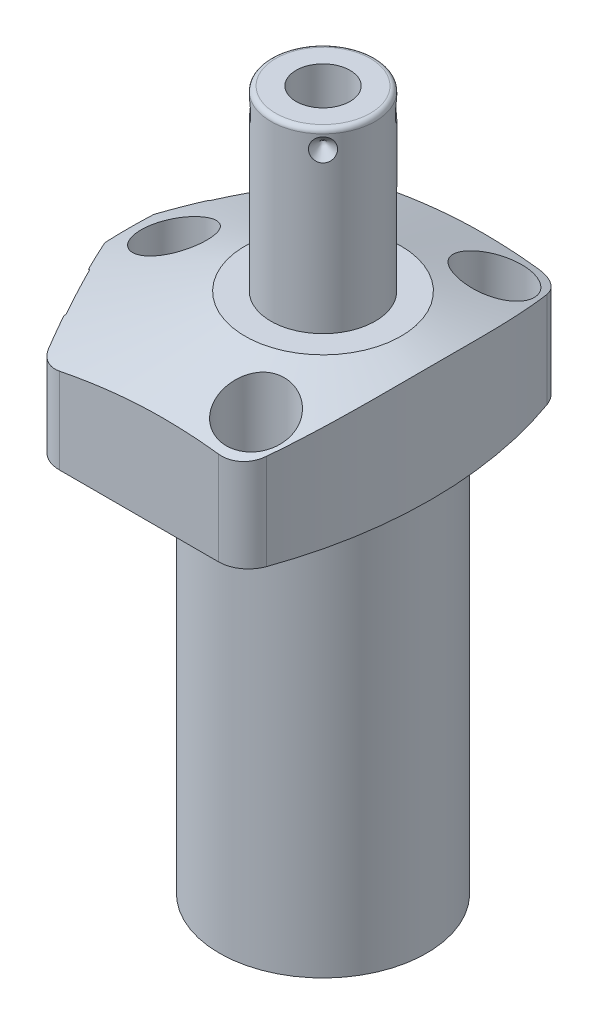
SolidWorks part; units mm, degrees
material "Alloy Steel"
ref_plane "Front Plane" through (0, 0, 0) normal (0, 0, 1) x (1, 0, 0)
ref_plane "Top Plane" through (0, 0, 0) normal (0, 1, 0) x (1, 0, 0)
ref_plane "Right Plane" through (0, 0, 0) normal (1, 0, 0) x (0, 0, -1)
ref_plane "Plane1" through (0, 0, 0) normal (0, 0, 1) x (0, -1, 0)
sketch "Sketch1" plane through (0, 0, 0) normal (0, 0, 1) x (0, -1, 0)
  line L0 (0, 44.45) -> (-26.9748, 44.45)
  line L1 (-26.9748, 44.45) -> (-26.9748, 0)
  line L2 (-26.9748, 0) -> (84.1502, 0)
  line L3 (84.1502, 0) -> (84.1502, 22.098)
  line L4 (84.1502, 22.098) -> (0, 22.098)
  line L5 (0, 22.098) -> (0, 44.45)
  line L6 (-32.531, 0) -> (89.7065, 0) construction
  dimension "D1" = 111.125
  dimension "D2" = 26.9748
  dimension "D3" = 88.9
  dimension "D4" = 44.196
revolve "Revolve1" add sketch "Sketch1" angle 360 about L6
ref_plane "Plane2" through (0, 0, 0) normal (0, -1, 0) x (0, 0, -1)
sketch "Sketch2" plane through (0, 0, 0) normal (0, -1, 0) x (0, 0, -1)
  line L0 (34.1122, -28.4984) -> (34.1122, 28.4984)
  line L2 (-34.1122, 28.4984) -> (-34.1122, -28.4984)
  line L3 (0, -32.1458) -> (0, 48.0974) construction
  arc A0 (34.1122, -28.4984) -> (34.1122, 28.4984) centre (0, 0) ccw
  circle A1 centre (0, 0) radius 44.45
  arc A2 (-34.1122, 28.4984) -> (-34.1122, -28.4984) centre (0, 0) ccw
  point P4 (0, 0)
  dimension "D1" = 68.2244
  dimension "D2" = 0
extrude "Cut-Extrude1" cut sketch "Sketch2" against normal up to next
ref_plane "Plane3" through (0, 0, 0) normal (0, -1, 0) x (-1, 0, 0)
sketch "Sketch3" plane through (0, 0, 0) normal (0, -1, 0) x (-1, 0, 0)
  line L0 (25.9049, 34.1122) -> (44.0427, 0)
  line L1 (44.0427, 0) -> (25.9049, -34.1122)
  line L2 (-39.4859, -20.995) -> (73.8214, 39.2515) construction
  line L3 (0, 0) -> (44.0427, 0) construction
  line L6 (-28.4984, -34.1122) -> (28.4984, -34.1122)
  line L7 (28.4984, 34.1122) -> (-28.4984, 34.1122)
  line L8 (25.9049, -34.1122) -> (28.4984, -34.1122)
  line L9 (28.4984, 34.1122) -> (25.9049, 34.1122)
  arc A2 (-28.4984, 34.1122) -> (-28.4984, -34.1122) centre (0, 0) ccw
  arc A3 (28.4984, -34.1122) -> (28.4984, 34.1122) centre (0, 0) ccw
  arc A5 (28.4984, -34.1122) -> (28.4984, 34.1122) centre (0, 0) ccw
  dimension "D1" = 28
  dimension "D2" = 38.8874
  dimension "D3" = 0
extrude "Cut-Extrude2" cut sketch "Sketch3" against normal up to next
ref_plane "Plane4" through (0, 0, 0) normal (0, -1, 0) x (-1, 0, 0)
sketch "S2D0002" plane through (0, 0, 0) normal (0, -1, 0) x (-1, 0, 0)
  line L0 (41.275, 85.425) -> (41.275, -85.425)
  arc A0 (41.275, 85.425) -> (41.275, -85.425) centre (65.8876, 0) ccw
  dimension "D3" = 88.9
  dimension "D1" = 65.8876
  dimension "D2" = 41.275
extrude "Cut-Extrude3" cut sketch "S2D0002" against normal blind 38.0873 flip side to cut
fillet "Fillet1" radius 6.35 2 edges at (16.2073, 13.4874, 34.1122) (16.2073, 13.4874, -34.1122)
fillet "Fillet2" radius 6.35 1 edges at (-25.9049, 13.4874, 34.1122)
fillet "Fillet3" radius 6.35 1 edges at (-25.9049, 13.4874, -34.1122)
ref_plane "Plane5" through (0, 0, 0) normal (0, 0, 1) x (1, 0, 0)
sketch "Sketch5" plane through (0, 0, 0) normal (0, 0, 1) x (1, 0, 0)
  line L0 (-16.637, 26.9748) -> (-47.625, 15.6961)
  line L1 (0, 7.6649) -> (0, 27.5963) construction
  line L3 (11.854, 26.9748) -> (-22.0895, 26.9748) construction
  line L4 (-16.637, 26.9748) -> (-47.625, 26.9748)
  line L5 (-47.625, 26.9748) -> (-47.625, 15.6961)
  dimension "D1" = 33.274
  dimension "D2" = 20
  dimension "D3" = 47.625
revolve "Cut-Revolve1" cut sketch "Sketch5" angle 360 about L1
ref_plane "Plane6" through (-34.1113, 10.287, -18.1373) normal (0, 1, 0) x (0.4695, 0, -0.8829)
sketch "Sketch6" plane through (-34.1113, 10.287, -18.1373) normal (0, 1, 0) x (0.4695, 0, -0.8829)
  line L0 (0, 0) -> (6.1849, 0)
  line L1 (6.1849, 0) -> (5.6423, -2.5527)
  line L2 (5.6423, -2.5527) -> (4.9784, -3.2166)
  line L3 (4.9784, -3.2166) -> (4.9784, -15.748)
  line L4 (4.9784, -15.748) -> (0, -15.748)
  line L5 (0, -15.748) -> (0, 0)
  line L6 (0, -16.5354) -> (0, 0.7874) construction
  dimension "D1" = 15.748
revolve "Cut-Revolve2" cut sketch "Sketch6" angle 360 about L6
ref_plane "Plane7" through (-34.1113, 10.287, 18.1373) normal (0, 1, 0) x (-0.4695, 0, -0.8829)
sketch "Sketch7" plane through (-34.1113, 10.287, 18.1373) normal (0, 1, 0) x (-0.4695, 0, -0.8829)
  line L0 (0, 0) -> (6.1849, 0)
  line L1 (6.1849, 0) -> (5.6423, -2.5527)
  line L2 (5.6423, -2.5527) -> (4.9784, -3.2166)
  line L3 (4.9784, -3.2166) -> (4.9784, -15.748)
  line L4 (4.9784, -15.748) -> (0, -15.748)
  line L5 (0, -15.748) -> (0, 0)
  line L6 (0, -16.5354) -> (0, 0.7874) construction
  dimension "D1" = 15.748
revolve "Cut-Revolve3" cut sketch "Sketch7" angle 360 about L6
ref_plane "Plane8" through (-13.4874, 2.667, -26.5938) normal (0, 0, 1) x (-1, 0, 0)
sketch "Sketch8" plane through (-13.4874, 2.667, -26.5938) normal (0, 0, 1) x (-1, 0, 0)
  line L0 (0, 0) -> (4.5466, 0)
  line L1 (4.5466, 0) -> (4.1066, -2.0701)
  line L2 (4.1066, -2.0701) -> (3.4544, -2.7223)
  line L3 (3.4544, -2.7223) -> (3.4544, -12.573)
  line L4 (3.4544, -12.573) -> (0, -12.573)
  line L5 (0, -12.573) -> (0, 0)
  line L6 (0, -13.2017) -> (0, 0.6287) construction
  dimension "D1" = 12.573
revolve "Cut-Revolve4" cut sketch "Sketch8" angle 360 about L6
ref_plane "Plane9" through (-13.4874, 2.667, 26.5938) normal (0, 0, 1) x (-1, 0, 0)
sketch "Sketch9" plane through (-13.4874, 2.667, 26.5938) normal (0, 0, 1) x (-1, 0, 0)
  line L0 (0, 0) -> (4.5466, 0)
  line L1 (4.5466, 0) -> (4.1066, -2.0701)
  line L2 (4.1066, -2.0701) -> (3.4544, -2.7223)
  line L3 (3.4544, -2.7223) -> (3.4544, -12.573)
  line L4 (3.4544, -12.573) -> (0, -12.573)
  line L5 (0, -12.573) -> (0, 0)
  line L6 (0, -13.2017) -> (0, 0.6287) construction
  dimension "D1" = 12.573
revolve "Cut-Revolve5" cut sketch "Sketch9" angle 360 about L6
sketch "Sketch17" plane through (-34.3355, 0, 18.2565) normal (-0.8829, 0, 0.4695) x (0.4695, 0, 0.8829)
  circle A0 centre (0, 10.287) radius 10.4775
  dimension "D1" = 20.955
extrude "Cut-Extrude4" cut sketch "Sketch17" against normal blind 0.254
sketch "Sketch18" plane through (0, 0, 0) normal (0, -1, 0) x (1, 0, 0)
  circle A0 centre (-13.4874, 26.5938) radius 5.5626
  dimension "D1" = 11.1252
extrude "Cut-Extrude5" cut sketch "Sketch18" against normal blind 2.667
mirror "Mirror1" about plane through (0, 0, 0) normal (0, 0, 1) of "Cut-Extrude5", "Cut-Extrude4"
ref_plane "Plane10" through (0, 0, 0) normal (1, 0, 0) x (0, 0, -1)
sketch "Sketch10" plane through (0, 0, 0) normal (1, 0, 0) x (0, 0, -1)
  line L0 (0, 26.9748) -> (-11.1125, 26.9748)
  line L1 (-11.1125, 26.9748) -> (-11.1125, 63.8302)
  line L2 (-10.0965, 64.8462) -> (0, 64.8462)
  line L3 (0, 64.8462) -> (0, 26.9748)
  line L4 (0, 14.3517) -> (0, 66.7398) construction
  line L5 (16.637, 26.9748) -> (-16.637, 26.9748) construction
  line L6 (-29.8978, 0) -> (29.8978, 0) construction
  arc A0 (-10.0965, 64.8462) -> (-11.1125, 63.8302) centre (-10.0965, 63.8302) ccw
  dimension "D2" = 1.016
  dimension "D1" = 64.8462
  dimension "D3" = 22.225
revolve "Revolve2" add sketch "Sketch10" angle 360 about L4
ref_plane "Plane11" through (5.7531, 64.8462, 0) normal (0, 0, 1) x (1, 0, 0)
sketch "S2D0001" plane through (5.7531, 64.8462, 0) normal (0, 0, 1) x (1, 0, 0)
  line L0 (0, 0) -> (0, -17.018)
  line L1 (0, -17.018) -> (-5.7531, -20.4748)
  line L2 (0, 0) -> (-5.7531, 0)
  line L3 (-5.7531, 0) -> (-5.7531, -20.4748)
  line L4 (-5.7531, -27.7363) -> (-5.7531, 1.0237) construction
  line L5 (4.3434, 0) -> (-15.8496, 0) construction
  dimension "D1" = 11.5062
  dimension "D2" = 17.018
  dimension "D3" = 59
revolve "Cut-Revolve6" cut sketch "S2D0001" angle 360 about L4
sketch "Sketch12" plane through (-34.1113, 0, -18.1373) normal (-0.8829, 0, -0.4695) x (-0.4695, 0, 0.8829)
  circle A0 centre (0, 10.287) radius 6.4389
  circle A1 centre (0, 10.287) radius 4.9784 construction
  dimension "D1" = 12.8778
extrude "Extrude1" add sketch "Sketch12" along normal blind 1.651
sketch "Sketch13" plane through (0, 0, 0) normal (0, -1, 0) x (1, 0, 0)
  circle A0 centre (-13.4874, -26.5938) radius 4.8006
  circle A1 centre (-13.4874, -26.5938) radius 3.4544 construction
  dimension "D1" = 9.6012
ref_plane "Plane12" through (-13.4874, 2.667, -26.5938) normal (0, 1, 0) x (-1, 0, 0)
extrude "Extrude2" add sketch "Sketch13" against normal up to surface
ref_plane "Plane13" through (-13.4874, 0, 26.5938) normal (1, 0, 0) x (0, 0, -1)
sketch "Sketch14" plane through (-13.4874, 0, 26.5938) normal (1, 0, 0) x (0, 0, -1)
  line L0 (5.461, 2.667) -> (5.461, 0.9398)
  line L1 (5.461, 0.9398) -> (5.3016, 0.9398)
  line L2 (2.667, 0.4318) -> (2.667, 0.127)
  line L3 (2.667, 0.127) -> (1.5875, 0.127)
  line L4 (1.5875, 0.127) -> (1.5875, 10.6172)
  line L5 (1.5875, 10.6172) -> (3.2512, 10.6172)
  line L6 (3.2512, 10.6172) -> (3.2512, 2.667)
  line L7 (3.2512, 2.667) -> (5.461, 2.667)
  line L8 (3.175, 0.9398) -> (3.8424, 0.9398)
  line L9 (0, -1.0109) -> (0, 11.1709) construction
  arc A0 (3.175, 0.9398) -> (2.667, 0.4318) centre (3.175, 0.4318) ccw
  arc A1 (3.8424, 0.9398) -> (5.3016, 0.9398) centre (4.572, 0.4318) ccw
  dimension "D1" = 2.54
  dimension "D2" = 7.9502
revolve "Revolve3" add sketch "Sketch14" angle 360 about L9
ref_plane "Plane14" through (-11.1125, 60.8838, 0) normal (0, 0, 1) x (0, 1, 0)
ref_plane "Plane15" through (0, 0, 0) normal (-0.7071, 0, 0.7071) x (0.7071, 0, 0.7071)
sketch "Sketch15" plane through (-7.8577, 60.8838, -7.8577) normal (-0.7071, 0, 0.7071) x (0, 1, 0)
  line L0 (0, 0) -> (2.413, 0)
  line L1 (2.413, 0) -> (0, -2.413)
  line L2 (0, 0) -> (0, -2.413)
  line L3 (0, -5.1094) -> (0, 0.1207) construction
  line L4 (2.9464, 0) -> (-33.909, 0) construction
  line L5 (3.9624, -21.209) -> (3.9624, -1.016) construction
  dimension "D1" = 3.9624
  dimension "D2" = 4.826
  dimension "D3" = 45
revolve "Cut-Revolve7" cut sketch "Sketch15" angle 360 about L3
pattern_circular "CirPattern1" count 4 over 360 about axis through (0, 14.3517, 0) along (0, -1, 0) of "Cut-Revolve7"
hole_wizard "Hole1" positions "Sketch20" profile "Sketch19" legacy end condition up to next
sketch "Sketch20" plane through (0, 26.9748, 0) normal (0, 1, 0) x (-1, 0, 0)
  line L0 (0, 0) -> (47.6205, 0) construction
  line L1 (0, 0) -> (0, 38.9977) construction
  point P0 (-11.1252, -25.4)
  point P10 (31.75, 0)
  point P14 (-11.1252, 25.4)
  dimension "D1" = 11.1252
  dimension "D2" = 25.4
  dimension "D3" = 31.75
sketch "Sketch19" plane through (11.1252, 26.9748, -25.4) normal (1, 0, 0) x (0, 0, 1)
  line L0 (0, 0) -> (0, 26.9748)
  line L1 (0, 26.9748) -> (4.3688, 26.9748)
  line L2 (4.3688, 26.9748) -> (4.3688, 16.6624)
  line L3 (4.3688, 16.6624) -> (6.9977, 16.6624)
  line L4 (6.9977, 16.6624) -> (6.9977, 0)
  line L5 (6.9977, 0) -> (0, 0)
  line L6 (0, 110) -> (0, -10) construction
  dimension "Diameter" = 8.7376
  dimension "Depth" = 26.9748
  dimension "C-Bore Diameter" = 13.9954
  dimension "C-Bore Depth" = 16.6624
